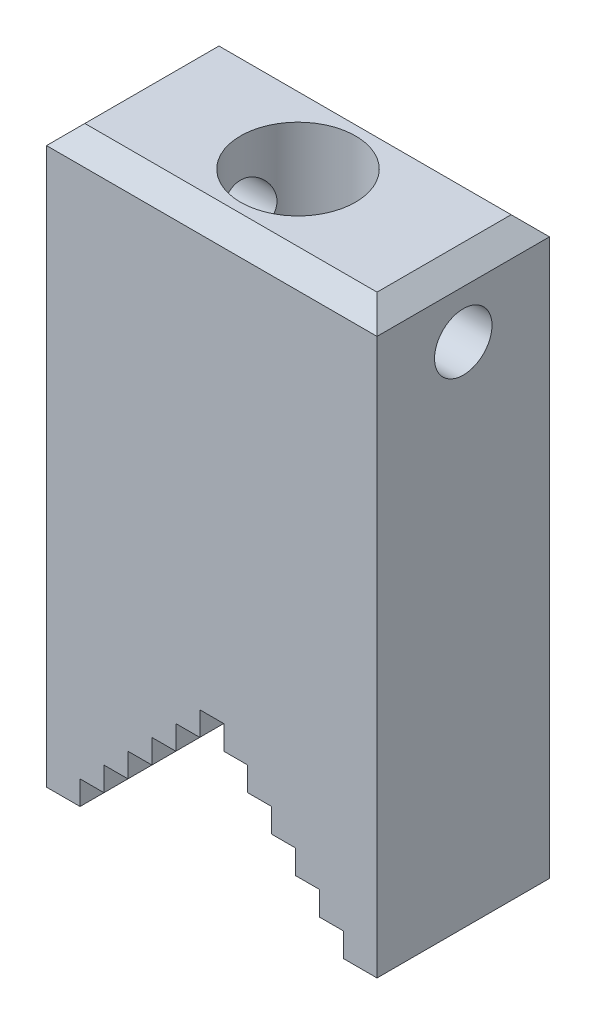
SolidWorks part; units mm, degrees
material "PBT General Purpose"
ref_plane "Front Plane" through (0, 0, 0) normal (0, 0, 1) x (1, 0, 0)
ref_plane "Top Plane" through (0, 0, 0) normal (0, 1, 0) x (1, 0, 0)
ref_plane "Right Plane" through (0, 0, 0) normal (1, 0, 0) x (0, 0, -1)
sketch "Sketch1" plane through (0, 0, 0) normal (0, 0, 1) x (1, 0, 0)
  line L0 (0, 0) -> (3.5, 0)
  line L1 (3.5, 0) -> (3.5, 2.5)
  line L2 (3.5, 2.5) -> (6, 2.5)
  line L3 (6, 2.5) -> (6, 5)
  line L4 (6, 5) -> (8.5, 5)
  line L5 (8.5, 5) -> (8.5, 7.5)
  line L6 (8.5, 7.5) -> (11, 7.5)
  line L7 (11, 7.5) -> (11, 10)
  line L8 (11, 10) -> (13.5, 10)
  line L9 (13.5, 10) -> (13.5, 12.5)
  line L10 (13.5, 12.5) -> (16, 12.5)
  line L11 (16, 12.5) -> (16, 15)
  line L12 (16, 15) -> (18.5, 15)
  line L13 (17.25, -3.1142) -> (17.25, 28.5001) construction
  line L14 (0, 0) -> (0, 60)
  line L15 (0, 60) -> (34.5, 60)
  line L16 (18.5, 12.5) -> (18.5, 15)
  line L17 (21, 12.5) -> (18.5, 12.5)
  line L18 (21, 10) -> (21, 12.5)
  line L19 (23.5, 10) -> (21, 10)
  line L20 (23.5, 7.5) -> (23.5, 10)
  line L21 (26, 7.5) -> (23.5, 7.5)
  line L22 (26, 5) -> (26, 7.5)
  line L23 (28.5, 5) -> (26, 5)
  line L24 (28.5, 2.5) -> (28.5, 5)
  line L25 (31, 2.5) -> (28.5, 2.5)
  line L26 (31, 0) -> (31, 2.5)
  line L27 (34.5, 0) -> (31, 0)
  line L28 (34.5, 0) -> (34.5, 60)
  point P20 (17.25, 15)
  point P33 (17.25, 60)
  dimension "D1" = 3.5
  dimension "D2" = 2.5
  dimension "D3" = 2.5
  dimension "D4" = 60
extrude "Boss-Extrude1" add sketch "Sketch1" along normal blind 18
ref_plane "Plane1" through (0, 0, 9) normal (0, 0, 1) x (1, 0, 0)
sketch "Sketch2" plane through (0, 0, 9) normal (0, 0, 1) x (1, 0, 0)
  line L0 (11.25, 60) -> (11.25, 40)
  line L1 (11.25, 60) -> (17.25, 60)
  line L2 (17.25, 60) -> (17.25, 36.5359)
  line L3 (34.5, 60) -> (0, 60) construction
  line L4 (16, 15) -> (18.5, 15) construction
  line L5 (11.25, 40) -> (17.25, 36.5359)
  line L6 (17.25, 31.4797) -> (17.25, 56.4173) construction
  point P13 (17.25, 60)
  dimension "D1" = 6
  dimension "D2" = 20
  dimension "D3" = 60
revolve "Cut-Revolve1" cut sketch "Sketch2" angle 360 about L2
sketch "Sketch3" plane through (34.5, 0, 0) normal (1, 0, 0) x (0, 0, -1)
  line L0 (-18, 60) -> (0, 60) construction
  circle A0 centre (-9, 53) radius 3
  point P4 (-9, 60)
  dimension "D1" = 7
  dimension "D2" = 6
extrude "Cut-Extrude1" cut sketch "Sketch3" against normal through all
chamfer "Chamfer2" distance 2 angle 45 4 edges at (0, 60, 9) (17.25, 60, 0) (17.25, 60, 18) (34.5, 60, 9)
